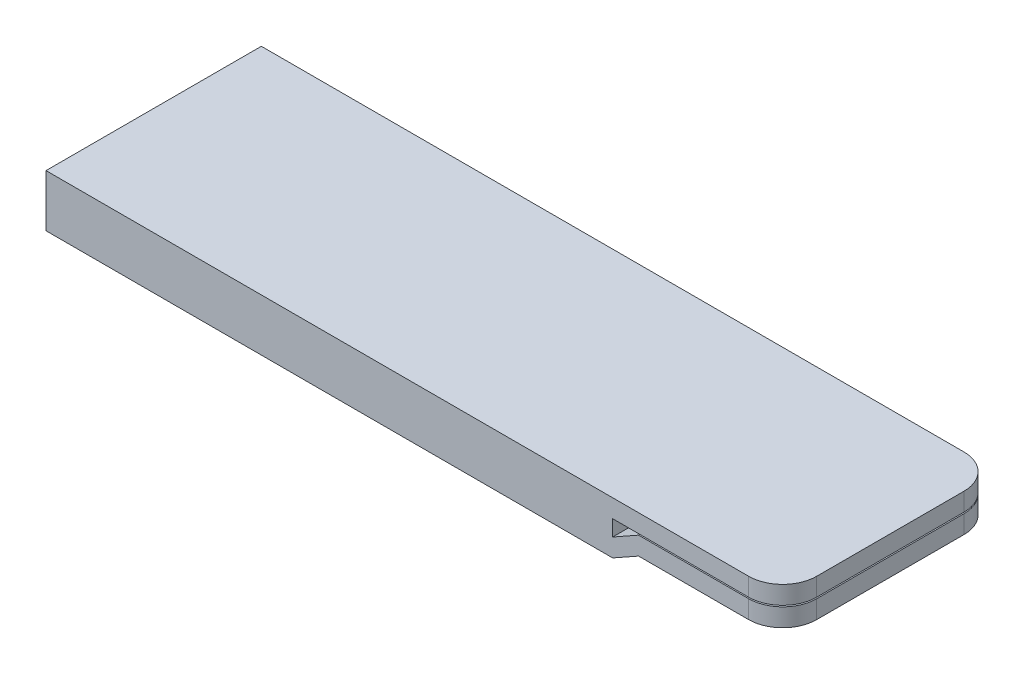
SolidWorks part; units mm, degrees
ref_plane "Front Plane" through (0, 0, 0) normal (0, 0, 1) x (1, 0, 0)
ref_plane "Top Plane" through (0, 0, 0) normal (0, 1, 0) x (1, 0, 0)
ref_plane "Right Plane" through (0, 0, 0) normal (1, 0, 0) x (0, 0, -1)
sketch "Sketch1" plane through (0, 0, 0) normal (0, 0, 1) x (1, 0, 0)
  line L0 (32.5, 0.7) -> (32.5, -0.7) construction
  line L1 (-32.5, 2.3) -> (32.5, 2.3)
  line L2 (-32.5, 2.3) -> (-32.5, -2.3)
  line L3 (-32.5, -2.3) -> (17.5, -2.3)
  line L4 (32.5, 2.3) -> (32.5, 0.7)
  line L5 (-32.5, 2.3) -> (19.1767, -1.3571) construction
  line L6 (-32.5, -2.3) -> (32.5, 2.3) construction
  line L7 (32.5, 0.7) -> (17.5, 0.7)
  line L8 (32.5, 0.7) -> (32.5, -0.7) construction
  line L9 (19.7845, -0.7) -> (17.5, -0.7) construction
  line L10 (17.5, 0.7) -> (17.5, -0.7)
  line L11 (32.5, -0.7) -> (32.5, -1.0154) construction
  line L12 (17.5, -2.3) -> (19.7845, -1.0154)
  line L13 (19.7845, -1.0154) -> (32.5, -1.0154)
  line L14 (32.5, -1.0154) -> (32.5, 0.5846)
  line L15 (32.5, 0.5846) -> (19.7845, 0.5846)
  line L16 (19.7845, 0.5846) -> (17.5, -0.7)
  line L17 (19.7845, -1.0154) -> (19.7845, -0.7)
  line L18 (17.5, -2.3) -> (32.5, -2.3) construction
  line L19 (19.1767, -1.3571) -> (32.5, -2.3) construction
  line L20 (32.5, -1.0154) -> (32.5, -2.3) construction
  line L21 (32.5, -0.7) -> (19.7845, -0.7) construction
  line L22 (19.7845, -0.7) -> (19.7845, 0.5846) construction
  point P0 (0, 0)
  point P10 (17.5, 0)
  dimension "D1" = 4.6
  dimension "D2" = 65
  dimension "D3" = 1.6
  dimension "D4" = 50
extrude "Boss-Extrude1" add sketch "Sketch1" along normal mid plane 19 contours L12 L3 L2 L1 L4 L7 L10 L16 L15 L14 L13
fillet "Fillet1" radius 3 4 edges at (32.5, 1.5, -9.5) (32.5, 1.5, 9.5) (32.5, -0.2154, -9.5) (32.5, -0.2154, 9.5)
